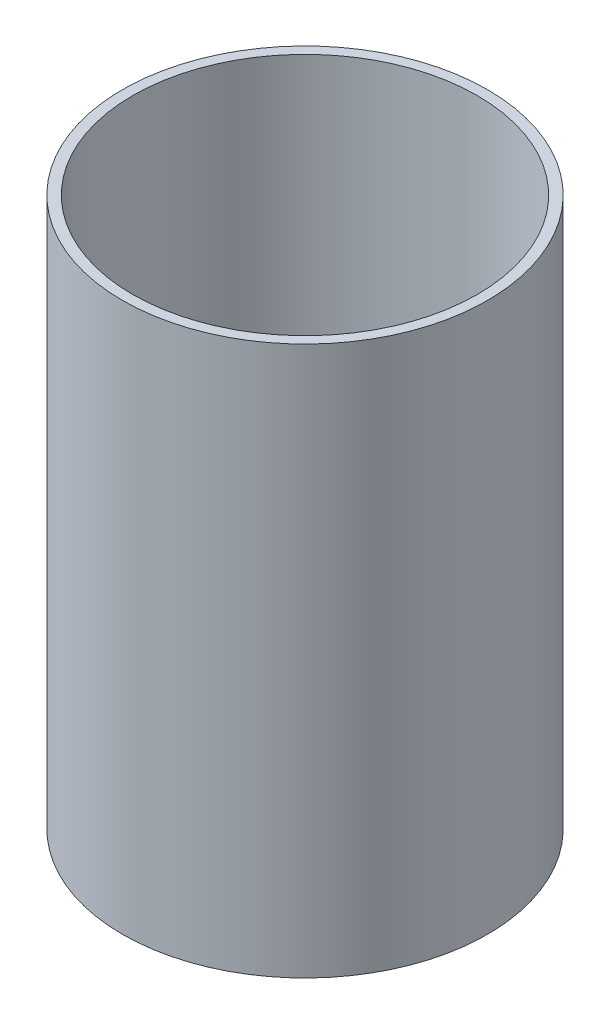
SolidWorks part; units mm, degrees
ref_plane "Front Plane" through (0, 0, 0) normal (0, 0, 1) x (1, 0, 0)
ref_plane "Top Plane" through (0, 0, 0) normal (0, 1, 0) x (1, 0, 0)
ref_plane "Right Plane" through (0, 0, 0) normal (1, 0, 0) x (0, 0, -1)
sketch "Sketch1" plane through (0, 0, 0) normal (0, 1, 0) x (1, 0, 0)
  circle A0 centre (0, 0) radius 25.3365
  circle A2 centre (0, 0) radius 23.9141
  dimension "D1" = 50.673
  dimension "D2" = 1.4224
extrude "Boss-Extrude1" add sketch "Sketch1" along normal blind 76.2
